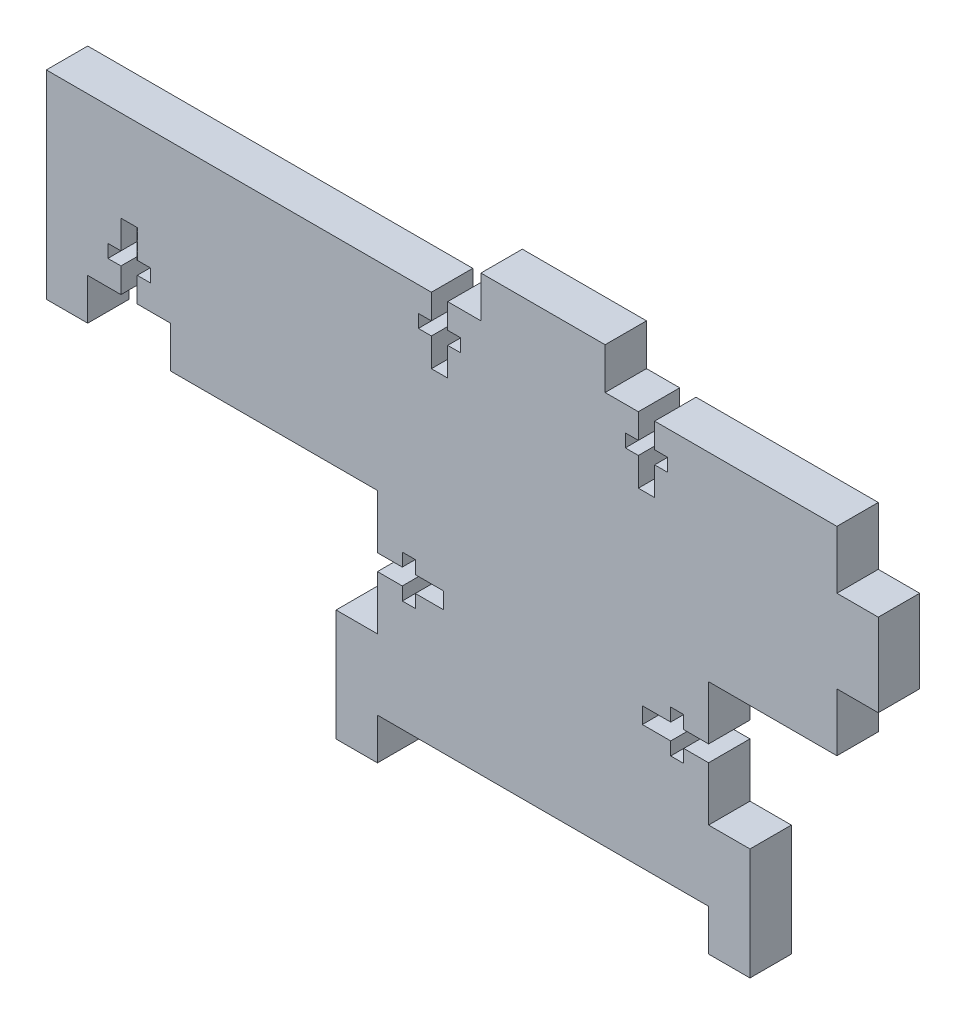
SolidWorks part; units mm, degrees
ref_plane "Front Plane" through (0, 0, 0) normal (0, 0, 1) x (1, 0, 0)
ref_plane "Top Plane" through (0, 0, 0) normal (0, 1, 0) x (1, 0, 0)
ref_plane "Right Plane" through (0, 0, 0) normal (1, 0, 0) x (0, 0, -1)
sketch "Sketch1" plane through (0, 0, 0) normal (0, 0, 1) x (1, 0, 0)
  line L0 (9.525, 66.675) -> (9.525, 0) construction
  line L1 (0, 0) -> (19.05, 0)
  line L2 (-15.875, 29.845) -> (-15.875, 10.795)
  line L3 (0, 66.675) -> (19.05, 66.675)
  line L4 (34.925, 29.845) -> (34.925, 10.795)
  line L5 (-66.675, 29.845) -> (-15.875, 29.845)
  line L6 (54.61, 29.845) -> (34.925, 29.845)
  line L7 (-15.875, 60.325) -> (0, 60.325)
  line L8 (0, 66.675) -> (0, 60.325)
  line L9 (-22.225, 10.795) -> (-15.875, 10.795)
  line L10 (41.275, 10.795) -> (34.925, 10.795)
  line L11 (34.925, 60.325) -> (19.05, 60.325)
  line L12 (19.05, 66.675) -> (19.05, 60.325)
  line L13 (34.925, 0) -> (34.925, -6.35)
  line L14 (60.96, 51.435) -> (54.61, 51.435)
  line L15 (-15.875, 0) -> (0, 0)
  line L16 (41.275, -6.35) -> (34.925, -6.35)
  line L17 (-22.225, 0) -> (-22.225, -6.35)
  line L18 (-22.225, -6.35) -> (-15.875, -6.35)
  line L19 (34.925, 0) -> (19.05, 0)
  line L20 (-15.875, 0) -> (-15.875, -6.35)
  line L21 (54.61, 51.435) -> (54.61, 60.325)
  line L22 (41.275, 0) -> (41.275, -6.35)
  line L23 (-15.875, 60.325) -> (-66.675, 60.325)
  line L25 (60.96, 38.735) -> (54.61, 38.735)
  line L26 (-66.675, 60.325) -> (-66.675, 29.845)
  line L27 (54.61, 29.845) -> (54.61, 38.735)
  line L29 (-22.225, 10.795) -> (-22.225, 0)
  line L35 (41.275, 0) -> (41.275, 10.795)
  line L36 (60.96, 38.735) -> (60.96, 51.435)
  line L37 (54.61, 60.325) -> (34.925, 60.325)
  dimension "D2" = 6.35
  dimension "D3" = 19.05
  dimension "D4" = 6.35
  dimension "D5" = 19.05
  dimension "D6" = 127.635
  dimension "D7" = 15.875
  dimension "D8" = 6.35
  dimension "D9" = 12.7
  dimension "D10" = 30.48
  dimension "D11" = 50.8
extrude "Boss-Extrude1" add sketch "Sketch1" along normal blind 6.35 contours L7 L8 L3 L12 L11 L37 L21 L14 L36 L25 L27 L6 L4 L10 L35 L22 L16 L13 L19 L1 L15 L20 L18 L17 L29 L9 L2 L5 L26 L23
sketch "Sketch2" plane through (0, 0, 6.35) normal (0, 0, 1) x (1, 0, 0)
  line L0 (-66.675, 29.845) -> (-15.875, 29.845) construction
  line L1 (-60.325, 29.845) -> (-47.625, 29.845)
  line L2 (-60.325, 29.845) -> (-60.325, 36.195)
  line L3 (-60.325, 36.195) -> (-47.625, 36.195)
  line L4 (-47.625, 29.845) -> (-47.625, 36.195)
  line L5 (-66.675, 60.325) -> (-66.675, 29.845) construction
  dimension "D1" = 12.7
  dimension "D2" = 6.35
  dimension "D3" = 6.35
extrude "Cut-Extrude1" cut sketch "Sketch2" against normal through all contours L3 L4 L1 L2
sketch "Sketch3" plane through (0, 0, 6.35) normal (0, 0, 1) x (1, 0, 0)
  line L0 (-15.875, 29.845) -> (-15.875, 10.795) construction
  line L1 (34.925, 29.845) -> (34.925, 10.795) construction
  line L2 (-15.875, 21.57) -> (-15.875, 19.07)
  line L3 (34.925, 21.57) -> (34.925, 19.07)
  line L13 (-15.875, 20.32) -> (-5.715, 20.32) construction
  line L14 (-15.875, 21.57) -> (-12.065, 21.57)
  line L17 (34.925, 19.07) -> (31.115, 19.07)
  line L18 (-15.875, 19.07) -> (-12.065, 19.07)
  line L21 (-5.715, 21.57) -> (-5.715, 19.07)
  line L22 (-10.065, 21.57) -> (-5.715, 21.57)
  line L24 (-10.065, 19.07) -> (-5.715, 19.07)
  line L25 (-12.065, 21.57) -> (-12.065, 23.57)
  line L27 (-12.065, 23.57) -> (-10.065, 23.57)
  line L28 (-10.065, 21.57) -> (-10.065, 23.57)
  line L33 (-12.065, 19.07) -> (-12.065, 17.07)
  line L34 (-12.065, 17.07) -> (-10.065, 17.07)
  line L38 (-10.065, 19.07) -> (-10.065, 17.07)
  line L39 (31.115, 19.07) -> (31.115, 17.07)
  line L40 (31.115, 17.07) -> (29.115, 17.07)
  line L41 (29.115, 19.07) -> (29.115, 17.07)
  line L42 (29.115, 19.07) -> (24.765, 19.07)
  line L43 (34.925, 20.32) -> (24.765, 20.32) construction
  line L44 (24.765, 21.57) -> (24.765, 19.07)
  line L45 (29.115, 21.57) -> (24.765, 21.57)
  line L46 (29.115, 21.57) -> (29.115, 23.57)
  line L47 (31.115, 23.57) -> (29.115, 23.57)
  line L48 (31.115, 21.57) -> (31.115, 23.57)
  line L49 (34.925, 21.57) -> (31.115, 21.57)
  point P2 (-15.875, 20.32)
  dimension "D2" = 3.81
  dimension "D3" = 10.16
  dimension "D9" = 2.5
  dimension "D10" = 2
extrude "Cut-Extrude2" cut sketch "Sketch3" against normal through all
sketch "Sketch5" plane through (0, 0, 6.35) normal (0, 0, 1) x (1, 0, 0)
  line L0 (9.525, 66.675) -> (9.525, 38.5617) construction
  line L1 (0, 66.675) -> (19.05, 66.675) construction
  line L2 (-7.6, 60.325) -> (-5.1, 60.325)
  line L3 (22.15, 56.515) -> (22.15, 54.515)
  line L4 (25.4, 60.325) -> (25.4, 50.165) construction
  line L5 (24.15, 60.325) -> (19.05, 60.325)
  line L6 (24.15, 54.515) -> (22.15, 54.515)
  line L7 (-15.875, 60.325) -> (-7.6, 60.325)
  line L8 (24.15, 56.515) -> (22.15, 56.515)
  line L9 (24.15, 54.515) -> (24.15, 50.165)
  line L10 (28.65, 54.515) -> (26.65, 54.515)
  line L11 (28.65, 56.515) -> (28.65, 54.515)
  line L12 (28.65, 56.515) -> (26.65, 56.515)
  line L13 (24.15, 60.325) -> (24.15, 56.515)
  line L14 (26.65, 50.165) -> (24.15, 50.165)
  line L15 (26.65, 60.325) -> (26.65, 56.515)
  line L16 (26.65, 54.515) -> (26.65, 50.165)
  line L17 (34.925, 60.325) -> (26.65, 60.325)
  line L18 (26.65, 60.325) -> (24.15, 60.325)
  line L19 (-60.325, 36.195) -> (-47.625, 36.195) construction
  line L20 (-55.225, 36.195) -> (-52.725, 36.195)
  line L21 (-55.225, 36.195) -> (-55.225, 40.005)
  line L22 (-55.225, 46.355) -> (-52.725, 46.355)
  line L23 (-52.725, 36.195) -> (-52.725, 40.005)
  line L24 (-55.225, 42.005) -> (-55.225, 46.355)
  line L25 (-52.725, 42.005) -> (-50.725, 42.005)
  line L26 (-53.975, 36.195) -> (-53.975, 46.355) construction
  line L27 (-52.725, 40.005) -> (-50.725, 40.005)
  line L28 (-50.725, 42.005) -> (-50.725, 40.005)
  line L29 (-55.225, 42.005) -> (-57.225, 42.005)
  line L30 (39.5511, 30.1625) -> (12.0576, 30.1625) construction
  line L31 (-55.225, 40.005) -> (-57.225, 40.005)
  line L32 (-57.225, 42.005) -> (-57.225, 40.005)
  line L33 (-52.725, 42.005) -> (-52.725, 46.355)
  line L34 (39.5511, 60.325) -> (39.5511, 0) construction
  line L35 (54.61, 60.325) -> (19.05, 60.325) construction
  line L36 (34.925, 0) -> (-15.875, 0) construction
  line L51 (-7.6, 54.515) -> (-7.6, 50.165)
  line L53 (-7.6, 60.325) -> (-7.6, 56.515)
  line L54 (-7.6, 50.165) -> (-5.1, 50.165)
  line L55 (-5.1, 60.325) -> (-5.1, 56.515)
  line L60 (-9.6, 56.515) -> (-7.6, 56.515)
  line L61 (-9.6, 56.515) -> (-9.6, 54.515)
  line L62 (-9.6, 54.515) -> (-7.6, 54.515)
  line L63 (-5.1, 54.515) -> (-5.1, 50.165)
  line L64 (-5.1, 56.515) -> (-3.1, 56.515)
  line L66 (-5.1, 54.515) -> (-3.1, 54.515)
  line L67 (-3.1, 56.515) -> (-3.1, 54.515)
  line L73 (-6.35, 60.325) -> (-6.35, 50.165) construction
  line L77 (-5.1, 60.325) -> (0, 60.325)
  point P26 (39.5511, 30.1625)
  dimension "D1" = 5.1
  dimension "D2" = 8.275
  dimension "D3" = 3.81
  dimension "D4" = 2
  dimension "D5" = 4.35
  dimension "D6" = 2
  dimension "D7" = 15.875
extrude "Cut-Extrude3" cut sketch "Sketch5" against normal through all contours L67 L64 L55 L2 L53 L60 L61 L62 L51 L54 L63 L66 | L25 L33 L22 L24 L29 L32 L31 L21 L20 L23 L27 L28 | L15 L18 L13 L8 L3 L6 L9 L14 L16 L10 L11 L12
